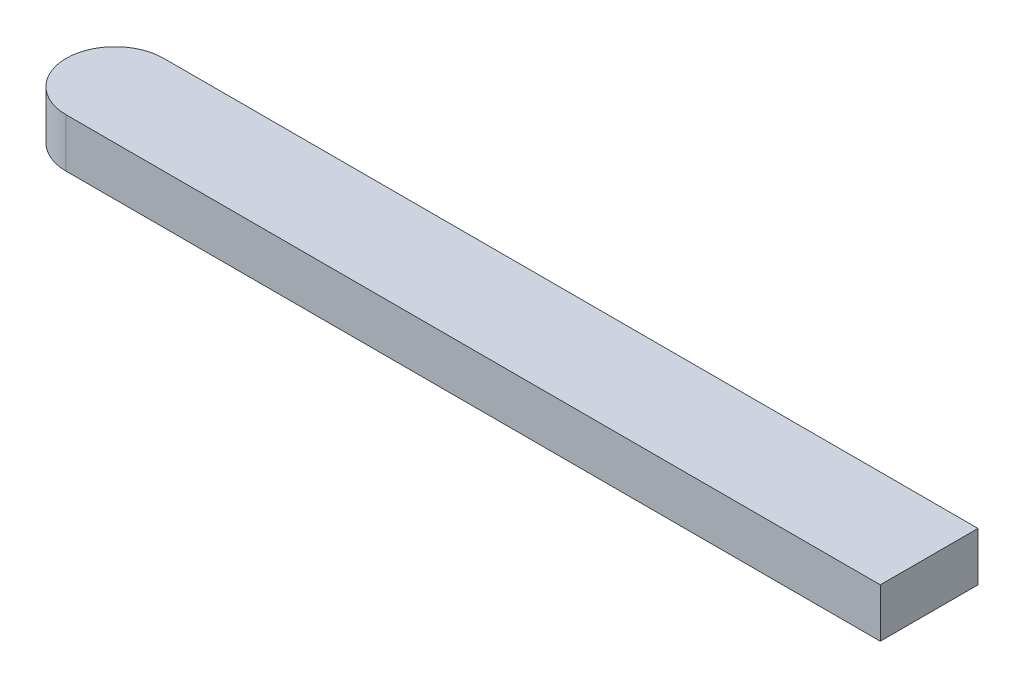
SolidWorks part; units mm, degrees
ref_plane "前视基准面" through (0, 0, 0) normal (0, 0, 1) x (1, 0, 0)
ref_plane "上视基准面" through (0, 0, 0) normal (0, 1, 0) x (1, 0, 0)
ref_plane "右视基准面" through (0, 0, 0) normal (1, 0, 0) x (0, 0, -1)
sketch "草图1" plane through (0, 0, 0) normal (0, 1, 0) x (1, 0, 0)
  line L1 (0, -3) -> (50, -3)
  line L2 (0, -3) -> (0, 3)
  line L3 (0, 3) -> (50, 3)
  line L4 (50, -3) -> (50, 3)
  circle A0 centre (0, 0) radius 3
extrude "凸台-拉伸1" add sketch "草图1" along normal blind 3 contours L2 A0
